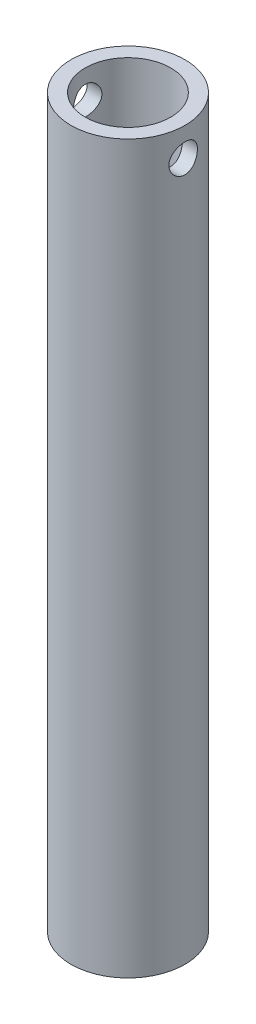
SolidWorks part; units mm, degrees
ref_plane "Front Plane" through (0, 0, 0) normal (0, 0, 1) x (1, 0, 0)
ref_plane "Top Plane" through (0, 0, 0) normal (0, 1, 0) x (1, 0, 0)
ref_plane "Right Plane" through (0, 0, 0) normal (1, 0, 0) x (0, 0, -1)
sketch "Sketch1" plane through (0, 0, 0) normal (0, 1, 0) x (1, 0, 0)
  circle A0 centre (0, 0) radius 12.7
  circle A1 centre (0, 0) radius 9.525
  dimension "D1" = 19.05
  dimension "D2" = 25.4
extrude "Boss-Extrude1" add sketch "Sketch1" along normal blind 161.925
sketch "Sketch2" plane through (0, 0, 0) normal (1, 0, 0) x (0, 0, -1)
  line L0 (0, 161.925) -> (0, 155.575) construction
  line L1 (9.525, 161.925) -> (-9.525, 161.925) construction
  circle A0 centre (0, 155.575) radius 3.175
  dimension "D1" = 6.35
  dimension "D2" = 6.35
extrude "Cut-Extrude1" cut sketch "Sketch2" against normal through all both and the other way through all
